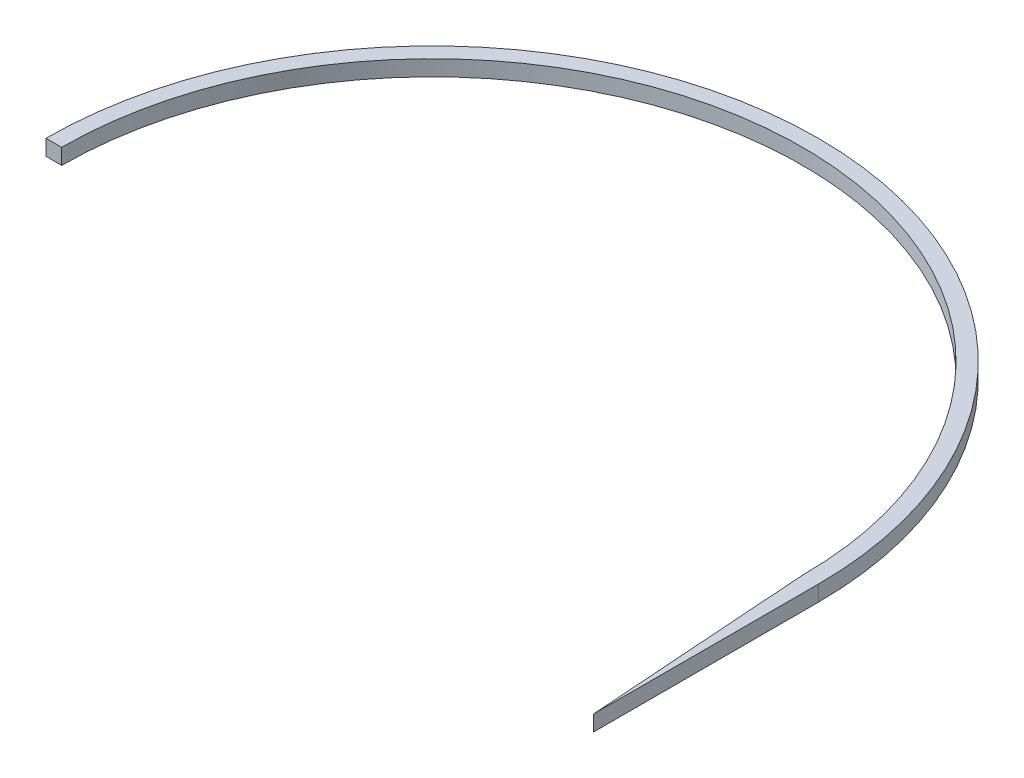
SolidWorks part; units mm, degrees
ref_plane "Front Plane" through (0, 0, 0) normal (0, 0, 1) x (1, 0, 0)
ref_plane "Top Plane" through (0, 0, 0) normal (0, 1, 0) x (1, 0, 0)
ref_plane "Right Plane" through (0, 0, 0) normal (1, 0, 0) x (0, 0, -1)
sketch "Sketch1" plane through (0, 0, 0) normal (0, 1, 0) x (1, 0, 0)
  line L0 (-280.7, 115) -> (-275, 115)
  line L1 (-5.7, 115) -> (0, 115) construction
  line L2 (-5.7, 115) -> (0, 115) construction
  line L3 (0, 115) -> (0, 33.3588)
  line L4 (0, 115) -> (-140.35, 115) construction
  line L5 (0, 33.3588) -> (-5.7, 115)
  arc A0 (0, 115) -> (-280.7, 115) centre (-140.35, 115) ccw
  arc A1 (-5.7, 115) -> (-275, 115) centre (-140.35, 115) ccw
  point P0 (0, 33.3588)
  dimension "D2" = 5.7
  dimension "D3" = 140.35
extrude "Boss-Extrude1" add sketch "Sketch1" along normal blind 5.7
